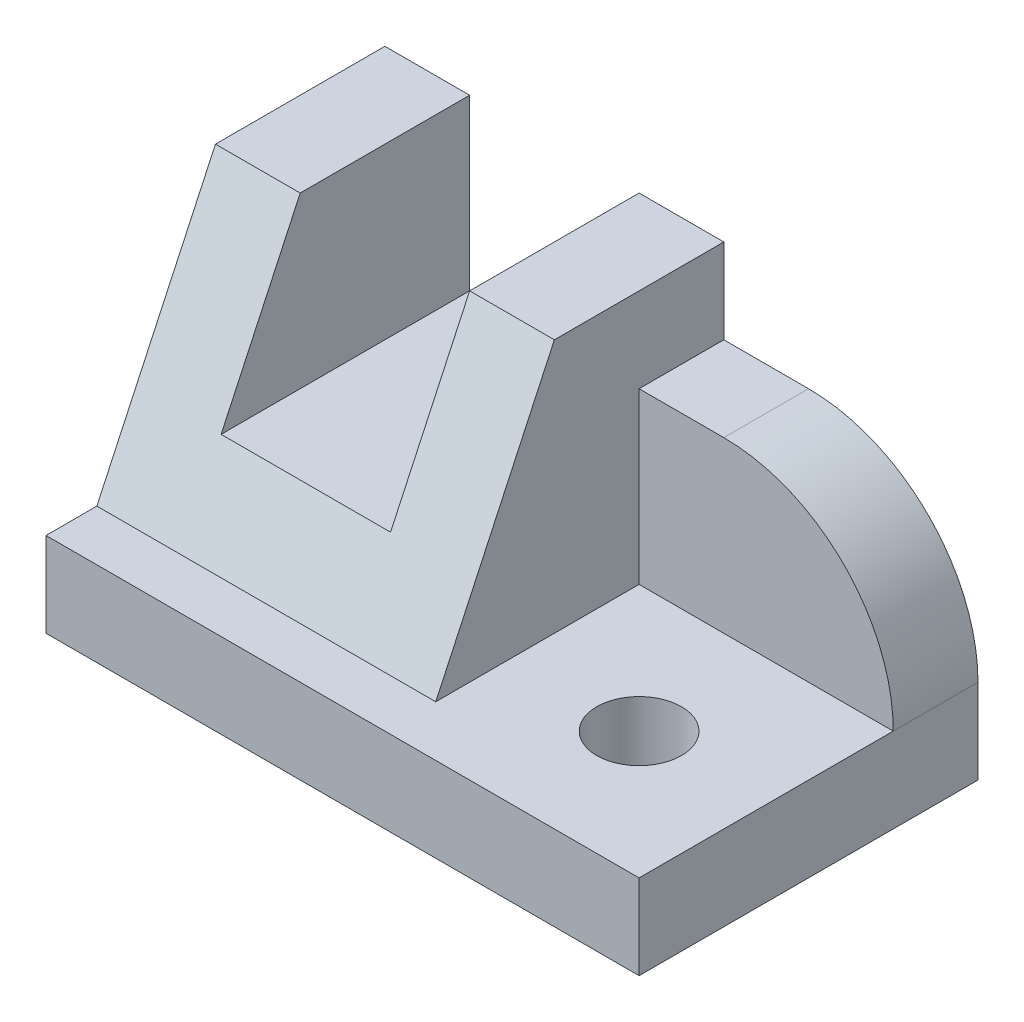
SolidWorks part; units mm, degrees
ref_plane "Front Plane" through (0, 0, 0) normal (0, 0, 1) x (1, 0, 0)
ref_plane "Top Plane" through (0, 0, 0) normal (0, 1, 0) x (1, 0, 0)
ref_plane "Right Plane" through (0, 0, 0) normal (1, 0, 0) x (0, 0, -1)
ref_plane "Plane1" through (0, 0, 0) normal (-1, 0, 0) x (0, -1, 0)
sketch "Sketch1" plane through (0, 0, 0) normal (-1, 0, 0) x (0, -1, 0)
  line L0 (-10, -6) -> (-40, -20)
  line L1 (-40, -20) -> (-10, -20)
  line L2 (-10, -20) -> (-10, -6)
  dimension "D1" = 30
  dimension "Width" = 14
extrude "Boss-Extrude1" add sketch "Sketch1" against normal blind 40
sketch "Sketch2" plane through (0, 0, -20) normal (0, 0, -1) x (-1, 0, 0)
  line L0 (-40, 40) -> (0, 40)
  line L1 (0, 40) -> (0, 10)
  line L2 (0, 10) -> (-40, 10)
  line L3 (-40, 10) -> (-40, 40)
extrude "Boss-Extrude2" add sketch "Sketch2" along normal blind 20
sketch "Sketch3" plane through (40, 0, 0) normal (1, 0, 0) x (0, 0, -1)
  line L0 (40, 10) -> (0, 10)
  line L1 (0, 10) -> (20, 40)
  line L2 (20, 40) -> (40, 40)
  line L3 (40, 40) -> (40, 10)
extrude "Boss-Extrude3" add sketch "Sketch3" along normal blind 30
sketch "Sketch4" plane through (70, 0, 0) normal (1, 0, 0) x (0, 0, -1)
  line L0 (20, 40) -> (0, 10)
  line L1 (0, 10) -> (30, 10)
  line L2 (30, 10) -> (30, 30)
  line L3 (30, 30) -> (40, 30)
  line L4 (40, 30) -> (40, 40)
  line L5 (40, 40) -> (20, 40)
extrude "Cut-Extrude1" cut sketch "Sketch4" against normal blind 30
sketch "Sketch5" plane through (0, 10, 0) normal (0, -1, 0) x (1, 0, 0)
  line L0 (70, 0) -> (70, -40)
  line L1 (70, -40) -> (0, -40)
  line L2 (0, -40) -> (0, 0)
  line L3 (0, 0) -> (70, 0)
extrude "Boss-Extrude4" add sketch "Sketch5" along normal blind 10
sketch "Sketch6" plane through (0, 0, -40) normal (0, 0, -1) x (-1, 0, 0)
  line L0 (-30, 40) -> (-30, 20)
  line L1 (-30, 20) -> (-10, 20)
  line L2 (-10, 20) -> (-10, 40)
  line L3 (-10, 40) -> (-30, 40)
extrude "Cut-Extrude2" cut sketch "Sketch6" against normal through all
hole_wizard "Ø10.0 (10) Diameter Hole1" positions "Sketch8" profile "Sketch7" hole size "Ø10.0" standard "ANSI Metric"
sketch "Sketch8" plane through (0, 0, 0) normal (0, -1, 0) x (-1, 0, 0)
  point P0 (-55, 15)
sketch "Sketch7" plane through (55, 0, -15) normal (1, 0, 0) x (0, 0, -1)
  line L0 (0, 0) -> (0, 40)
  line L1 (0, 40) -> (5, 40)
  line L2 (5, 40) -> (5, 0)
  line L5 (5, 0) -> (0, 0)
  line L11 (0, -6.35) -> (0, 107.95) construction
  dimension "Thru Hole Dia." = 10
  dimension "Thru Hole Depth" = 40
fillet "Fillet1" radius 20 1 edges at (70, 30, -35)
